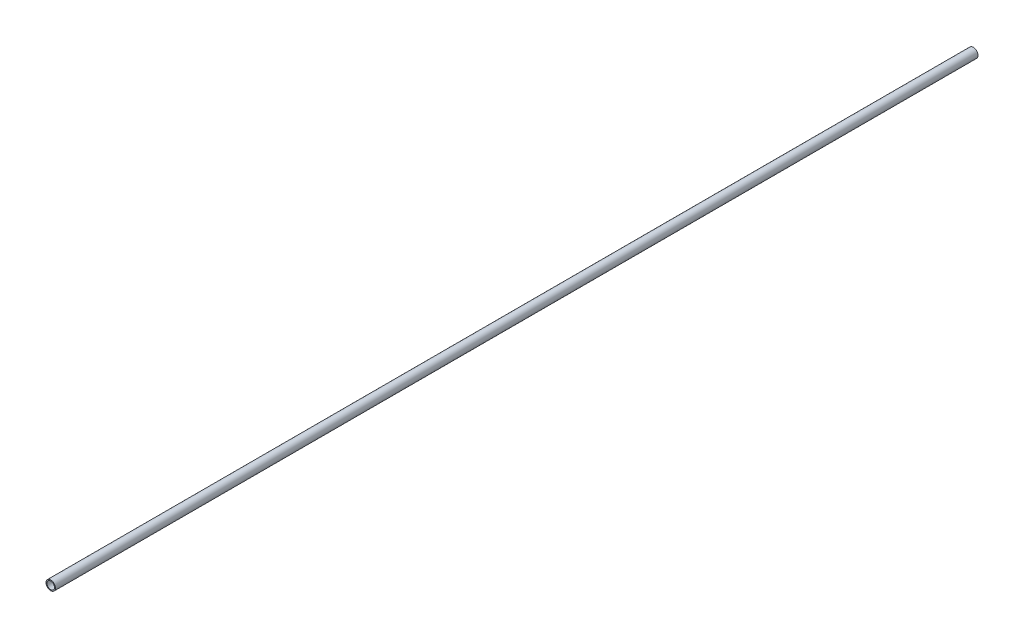
SolidWorks part; units mm, degrees
material "Hexcel AS4C (3000 Filaments)"
ref_plane "Front Plane" through (0, 0, 0) normal (0, 0, 1) x (1, 0, 0)
ref_plane "Top Plane" through (0, 0, 0) normal (0, 1, 0) x (1, 0, 0)
ref_plane "Right Plane" through (0, 0, 0) normal (1, 0, 0) x (0, 0, -1)
sketch "Sketch1" plane through (0, 0, 0) normal (0, 0, 1) x (1, 0, 0)
  circle A0 centre (0, 0) radius 6.35
  circle A1 centre (0, 0) radius 5.08
  dimension "D1" = 12.7
  dimension "D2" = 10.16
extrude "Boss-Extrude1" add sketch "Sketch1" along normal blind 1244.6
sketch "Sketch2" plane through (0, 0, 1244.6) normal (0, 0, 1) x (1, 0, 0)
  circle A0 centre (0, 0) radius 6.35 construction
  point P0 (0, -6.35)
ref_plane "LeftSupport" through (0, 0, 1231.9) normal (0, 0, 1) x (1, 0, 0)
ref_plane "RightSuppor" through (0, 0, 12.7) normal (0, 0, -1) x (-1, 0, 0)
ref_plane "Plane3" through (0, 6.35, 0) normal (0, 1, 0) x (1, 0, 0)
sketch "Roller1" plane through (0, 6.35, 0) normal (0, 1, 0) x (1, 0, 0)
  circle A0 centre (0, -12.7) radius 3.175
  dimension "D1" = 6.35
  dimension "D2" = 12.7
sketch "Roller2" plane through (0, 6.35, 0) normal (0, 1, 0) x (1, 0, 0)
  line L0 (-6.35, -1244.6) -> (6.35, -1244.6) construction
  circle A0 centre (0, -1231.9) radius 3.175
  dimension "D1" = 6.35
  dimension "D2" = 12.7
